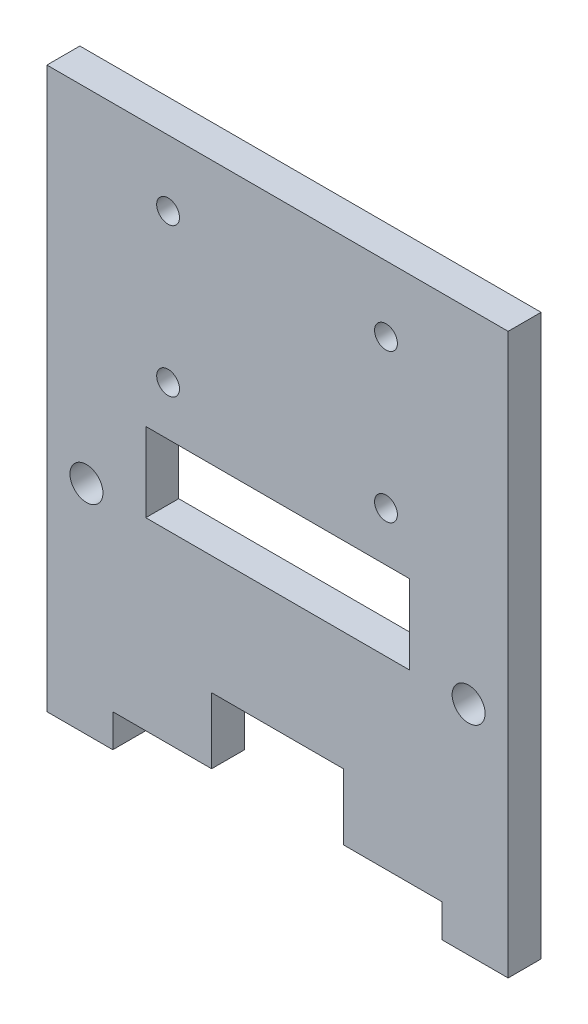
SolidWorks part; units mm, degrees
ref_plane "Front Plane" through (0, 0, 0) normal (0, 0, 1) x (1, 0, 0)
ref_plane "Top Plane" through (0, 0, 0) normal (0, 1, 0) x (1, 0, 0)
ref_plane "Right Plane" through (0, 0, 0) normal (1, 0, 0) x (0, 0, -1)
sketch "Sketch1" plane through (0, 0, 0) normal (0, 0, 1) x (1, 0, 0)
  line L1 (0, 0) -> (44.45, 0)
  line L2 (0, 0) -> (0, 53.975)
  line L3 (0, 53.975) -> (44.45, 53.975)
  line L4 (44.45, 0) -> (44.45, 53.975)
  dimension "D1" = 44.45
  dimension "D2" = 53.975
extrude "Boss-Extrude1" add sketch "Sketch1" along normal blind 3.175
sketch "Sketch2" plane through (0, 0, 3.175) normal (0, 0, 1) x (1, 0, 0)
  line L0 (0, 0) -> (44.45, 0) construction
  line L1 (6.35, 0) -> (38.1, 0)
  line L2 (6.35, 0) -> (6.35, 3.175)
  line L3 (6.35, 3.175) -> (38.1, 3.175)
  line L4 (38.1, 0) -> (38.1, 3.175)
  line L5 (0, 53.975) -> (0, 0) construction
  line L6 (44.45, 0) -> (44.45, 53.975) construction
  dimension "D1" = 6.35
  dimension "D2" = 6.35
  dimension "D3" = 3.175
extrude "Cut-Extrude1" cut sketch "Sketch2" against normal through all
sketch "Sketch3" plane through (0, 0, 3.175) normal (0, 0, 1) x (1, 0, 0)
  line L0 (0, 20.955) -> (44.45, 20.955) construction
  line L1 (0, 53.975) -> (0, 0) construction
  line L2 (44.45, 53.975) -> (0, 53.975) construction
  line L3 (22.225, 53.975) -> (22.225, 3.175) construction
  line L4 (38.1, 3.175) -> (6.35, 3.175) construction
  line L5 (44.45, 0) -> (44.45, 53.975) construction
  line L6 (0, 0) -> (6.35, 0) construction
  line L7 (15.875, 3.175) -> (28.575, 3.175)
  line L8 (15.875, 3.175) -> (15.875, 9.525)
  line L9 (15.875, 9.525) -> (28.575, 9.525)
  line L10 (28.575, 3.175) -> (28.575, 9.525)
  line L12 (9.525, 28.575) -> (34.925, 28.575)
  line L13 (9.525, 28.575) -> (9.525, 20.955)
  line L14 (9.525, 20.955) -> (34.925, 20.955)
  line L15 (34.925, 28.575) -> (34.925, 20.955)
  circle A0 centre (3.81, 20.955) radius 1.5875
  circle A1 centre (40.64, 20.955) radius 1.5875
  circle A2 centre (11.6772, 47.625) radius 1.1
  circle A3 centre (11.6772, 33.325) radius 1.1
  circle A4 centre (32.6772, 47.625) radius 1.1
  circle A5 centre (32.6772, 33.325) radius 1.1
  point P28 (34.925, 24.765)
  dimension "D2" = 3.175
  dimension "D3" = 18.415
  dimension "D9" = 2.2
  dimension "D1" = 20.955
  dimension "D4" = 6.35
  dimension "D5" = 12.7
  dimension "D6" = 6.35
  dimension "D7" = 14.3
  dimension "D8" = 21
  dimension "D10" = 6.35
  dimension "D11" = 7.62
  dimension "D12" = 25.4
  dimension "D13" = 12.7
extrude "Cut-Extrude2" cut sketch "Sketch3" against normal through all
